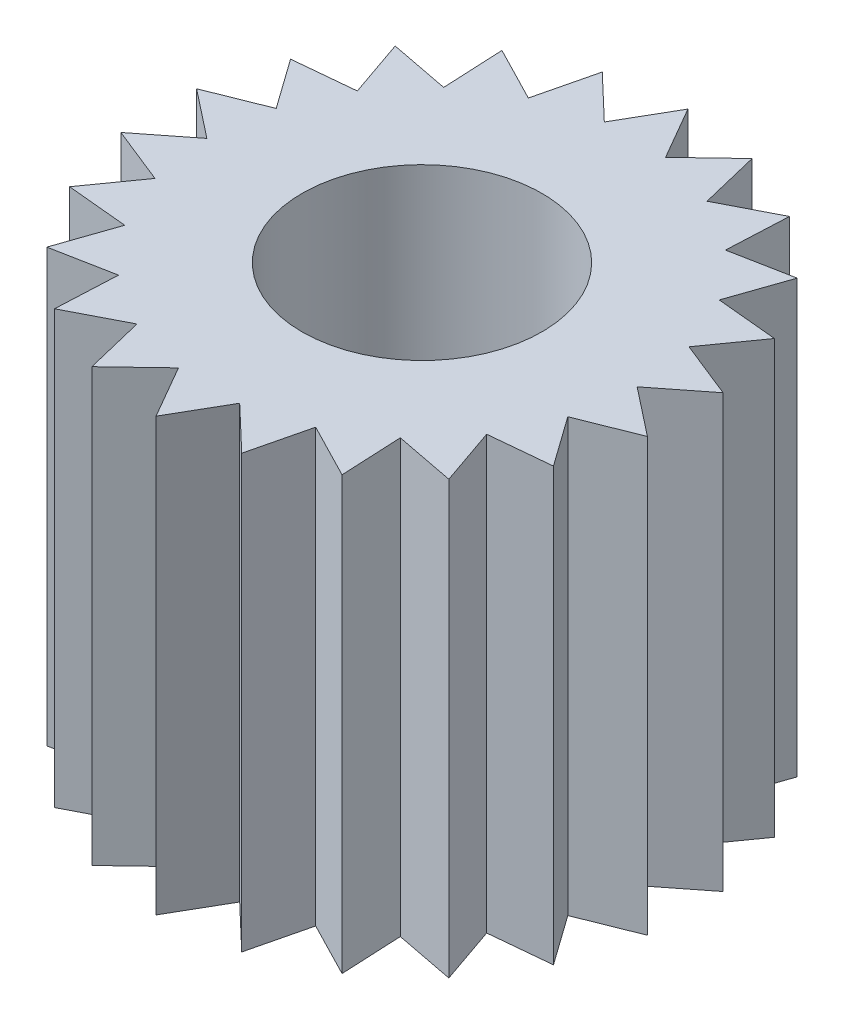
SolidWorks part; units mm, degrees
ref_plane "Front Plane" through (0, 0, 0) normal (0, 0, 1) x (1, 0, 0)
ref_plane "Top Plane" through (0, 0, 0) normal (0, 1, 0) x (1, 0, 0)
ref_plane "Right Plane" through (0, 0, 0) normal (1, 0, 0) x (0, 0, -1)
sketch "Sketch1" plane through (0, 0, 0) normal (0, 1, 0) x (1, 0, 0)
  line L0 (0, 8.0435) -> (0, 5.5413) construction
  line L1 (-8.4592, 0) -> (-5, 0) construction
  line L2 (1.5612, 5.3168) -> (0.6379, 4.4364)
  line L3 (0, 5.5413) -> (-0.6379, 4.4364)
  line L4 (-2.9412, -3.515) -> (-2.9351, -3.3873)
  line L5 (0.6379, 4.4364) -> (0, 5.5413)
  line L6 (2.9412, 3.515) -> (2.9351, 3.3873)
  line L7 (1.8619, 4.077) -> (1.5612, 5.3168)
  line L8 (2.9958, 4.6616) -> (1.8619, 4.077)
  line L9 (3.0013, 3.4001) -> (2.9351, 3.3873)
  line L10 (2.9412, 3.515) -> (2.9958, 4.6616)
  line L11 (4.1878, 3.6288) -> (3.0013, 3.4001)
  line L13 (3.7706, 2.4232) -> (4.1878, 3.6288)
  line L14 (5.0405, 2.3019) -> (3.7706, 2.4232)
  line L16 (4.3005, 1.2627) -> (5.0405, 2.3019)
  line L17 (5.4849, 0.7886) -> (4.3005, 1.2627)
  line L19 (4.4821, 0) -> (5.4849, 0.7886)
  line L20 (5.4849, -0.7886) -> (4.4821, 0)
  line L22 (4.3005, -1.2627) -> (5.4849, -0.7886)
  line L23 (5.0405, -2.3019) -> (4.3005, -1.2627)
  line L25 (3.7706, -2.4232) -> (5.0405, -2.3019)
  line L26 (4.1878, -3.6288) -> (3.7706, -2.4232)
  line L28 (2.9351, -3.3873) -> (4.1878, -3.6288)
  line L29 (2.9958, -4.6616) -> (2.9351, -3.3873)
  line L31 (1.8619, -4.077) -> (2.9958, -4.6616)
  line L32 (1.5612, -5.3168) -> (1.8619, -4.077)
  line L34 (0.6379, -4.4364) -> (1.5612, -5.3168)
  line L35 (0, -5.5413) -> (0.6379, -4.4364)
  line L37 (-0.6379, -4.4364) -> (0, -5.5413)
  line L38 (-1.5612, -5.3168) -> (-0.6379, -4.4364)
  line L40 (-1.8619, -4.077) -> (-1.5612, -5.3168)
  line L41 (-2.9958, -4.6616) -> (-1.8619, -4.077)
  line L43 (-2.9412, -3.515) -> (-2.9958, -4.6616)
  line L44 (-4.1878, -3.6288) -> (-2.9351, -3.3873)
  line L46 (-3.7706, -2.4232) -> (-4.1878, -3.6288)
  line L47 (-5.0405, -2.3019) -> (-3.7706, -2.4232)
  line L49 (-4.3005, -1.2627) -> (-5.0405, -2.3019)
  line L50 (-5.4849, -0.7886) -> (-4.3005, -1.2627)
  line L52 (-4.4821, 0) -> (-5.4849, -0.7886)
  line L53 (-5.4849, 0.7886) -> (-4.4821, 0)
  line L55 (-4.3005, 1.2627) -> (-5.4849, 0.7886)
  line L56 (-5.0405, 2.3019) -> (-4.3005, 1.2627)
  line L58 (-3.7706, 2.4232) -> (-5.0405, 2.3019)
  line L59 (-4.1878, 3.6288) -> (-3.7706, 2.4232)
  line L61 (-2.9351, 3.3873) -> (-4.1878, 3.6288)
  line L62 (-2.9958, 4.6616) -> (-2.9351, 3.3873)
  line L64 (-1.8619, 4.077) -> (-2.9958, 4.6616)
  line L65 (-1.5612, 5.3168) -> (-1.8619, 4.077)
  line L67 (-0.6379, 4.4364) -> (-1.5612, 5.3168)
  line L69 (0, 2.5) -> (0, -2.5) construction
  line L71 (5, 0) -> (11.8803, 0) construction
  line L72 (0, -5.5413) -> (0, -8.1568) construction
  line L76 (-2.5, 0) -> (2.5, 0) construction
  line L94 (0.772, 4.7294) -> (0.991, 4.7294) [skipped]
  circle A1 centre (0, 0) radius 2.5
  point P80 (0, 0)
  dimension "D1" = 5
  dimension "D4" = 22
extrude "Boss-Extrude1" add sketch "Sketch1" along normal blind 9
